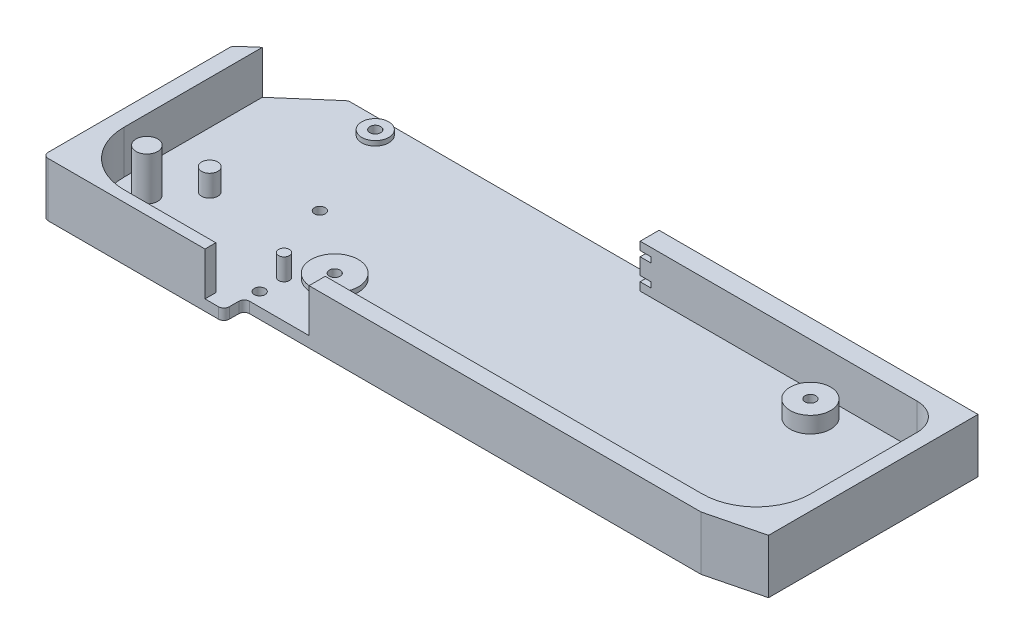
SolidWorks part; units mm, degrees
ref_plane "Front Plane" through (0, 0, 0) normal (0, 0, 1) x (1, 0, 0)
ref_plane "Top Plane" through (0, 0, 0) normal (0, 1, 0) x (1, 0, 0)
ref_plane "Right Plane" through (0, 0, 0) normal (1, 0, 0) x (0, 0, -1)
sketch "Sketch1" plane through (0, 0, 0) normal (0, 1, 0) x (1, 0, 0)
  line L0 (0, 0) -> (-23, -20)
  line L1 (-23, -20) -> (-23, -90)
  line L2 (0, 0) -> (233, 0)
  line L3 (233, 0) -> (233, -77.5)
  line L4 (44, -90) -> (-23, -90)
  line L7 (213, -82.5) -> (44, -82.5)
  line L8 (44, -82.5) -> (44, -90)
  line L10 (213, -82.5) -> (233, -77.5)
  circle A1 centre (16, -6) radius 2
  circle A2 centre (30, -40.5) radius 2
  circle A3 centre (54.5, -59.5) radius 2
  circle A4 centre (44.75, -77.5) radius 2
  circle A6 centre (187, -16) radius 2
  point P18 (187, -16)
  point P22 (44.75, -77.5)
  dimension "D1" = 4
  dimension "D4" = 4
  dimension "D7" = 4
  dimension "D10" = 4
  dimension "D15" = 4
  dimension "D23" = 20
  dimension "D2" = 16
  dimension "D3" = 6
  dimension "D5" = 34.5
  dimension "D6" = 14
  dimension "D8" = 24.5
  dimension "D9" = 19
  dimension "D11" = 18
  dimension "D12" = 14.75
  dimension "D16" = 43.5
  dimension "D17" = 132.5
  dimension "D18" = 256
  dimension "D19" = 67
  dimension "D20" = 20
  dimension "D21" = 90
  dimension "D22" = 23
  dimension "D24" = 5
  dimension "D25" = 7.5
extrude "Primary" add sketch "Sketch1" along normal blind 4
sketch "Sketch3" plane through (0, 4, 0) normal (0, 1, 0) x (1, 0, 0)
  circle A2 centre (3.5, -54.75) radius 3
  circle A3 centre (44.75, -68.5) radius 2
  circle A4 centre (44.75, -77.5) radius 2 construction
  point P11 (44.75, -77.5)
  dimension "D1" = 54.75
  dimension "D3" = 6
  dimension "D4" = 4
  dimension "D5" = 9
  dimension "D6" = 3.5
extrude "Stop Ext" add sketch "Sketch3" along normal blind 8
sketch "Sketch4" plane through (0, 4, 0) normal (0, 1, 0) x (1, 0, 0)
  line L1 (233, 0) -> (115, 0)
  line L3 (217.5, -7) -> (115, -7)
  line L4 (115, 0) -> (115, -7)
  line L11 (227.5, -56.5) -> (227.5, -17)
  line L17 (233, 0) -> (233, -77.5)
  line L18 (213, -82.5) -> (68, -82.5)
  line L19 (213, -82.5) -> (44, -82.5) construction
  line L20 (68, -82.5) -> (68, -76.5)
  line L21 (68, -76.5) -> (207.5, -76.5)
  line L22 (213, -82.5) -> (233, -77.5)
  arc A2 (207.5, -76.5) -> (227.5, -56.5) centre (207.5, -56.5) ccw
  arc A3 (227.5, -17) -> (217.5, -7) centre (217.5, -17) ccw
  point P2 (187, -16)
  point P13 (227.5, -8)
  point P15 (227.5, -7)
  point P23 (227.5, -76.5)
  dimension "D3" = 5.5
  dimension "D8" = 20
  dimension "D4" = 10
  dimension "D1" = 6
  dimension "D2" = 7
  dimension "D5" = 165
  dimension "D6" = 8
  dimension "D7" = 115
extrude "Front Ext" add sketch "Sketch4" along normal blind 16
sketch "Sketch5" plane through (0, 0, 0) normal (0, 0, -1) x (-1, 0, 0)
  line L0 (-115, 4) -> (-115, 20) construction
  line L2 (-115, 7) -> (-119, 7)
  line L3 (-115, 7) -> (-115, 9)
  line L4 (-115, 9) -> (-119, 9)
  line L5 (-119, 7) -> (-119, 9)
  line L6 (-115, 15) -> (-119, 15)
  line L7 (-115, 15) -> (-115, 17)
  line L8 (-115, 17) -> (-119, 17)
  line L9 (-119, 15) -> (-119, 17)
  line M12 (-115, 4) -> (-115, 20)
  dimension "D1" = 2
  dimension "D2" = 2
  dimension "D3" = 6
  dimension "D4" = 3
  dimension "D5" = 4
extrude "Cut-Extrude1" cut sketch "Sketch5" along normal through all from surface at -7 contours L9 L6 L8 M12
sketch "Sketch6" plane through (0, 0, 0) normal (0, 0, -1) x (-1, 0, 0)
  line L0 (-115, 15) -> (-119, 15) construction
  line L1 (-119, 9) -> (-117, 9)
  line L2 (-119, 9) -> (-119, 15)
  line L3 (-119, 15) -> (-117, 15)
  line L4 (-117, 9) -> (-117, 15)
  dimension "D1" = 2
extrude "Cut-Extrude2" cut sketch "Sketch6" against normal blind 3
sketch "Sketch7" plane through (0, 4, 0) normal (0, 1, 0) x (1, 0, 0)
  circle A1 centre (187, -16) radius 2
  circle A2 centre (187, -16) radius 7.5
  point P1 (187, -16)
  dimension "D1" = 4
  dimension "D2" = 15
extrude "Swingybit_Pin Ext" add sketch "Sketch7" along normal blind 6
sketch "Sketch8" plane through (0, 4, 0) normal (0, 1, 0) x (1, 0, 0)
  circle A0 centre (16, -6) radius 2
  circle A1 centre (16, -6) radius 5
  circle A2 centre (54.5, -59.5) radius 8.75
  circle A4 centre (54.5, -59.5) radius 2
  circle A5 centre (54.5, -59.5) radius 2 construction
  point P0 (16, -6)
  point P5 (30, -40.5)
  point P6 (54.5, -59.5)
  point P8 (-79.4755, -32.6714)
  dimension "D1" = 4
  dimension "D2" = 10
  dimension "D3" = 17.5
extrude "Wheel_Pin Ext" add sketch "Sketch8" along normal blind 1.75 contours A1 | A0 | A2 | A4
sketch "Sketch9" plane through (0, 4, 0) normal (0, 1, 0) x (1, 0, 0)
  line L0 (-23, -20) -> (-23, -86)
  line L1 (-23, -90) -> (37, -90)
  line L2 (-23, -90) -> (-23, -86)
  line L3 (3, -86) -> (37, -86)
  line L4 (37, -90) -> (37, -86)
  line L5 (-17, -66) -> (-17, -14.7826)
  line L6 (0, 0) -> (-23, -20) construction
  line L7 (-17, -14.7826) -> (-23, -20)
  arc A0 (3, -86) -> (-17, -66) centre (3, -66) cw
  point P12 (-17, -86)
  point P14 (-17, -86)
  dimension "D4" = 20
  dimension "D1" = 4
  dimension "D2" = 60
  dimension "D3" = 6
extrude "Bottom Ext" add sketch "Sketch9" along normal blind 16
fillet "Fillet1" radius 2 5 edges at (44, 2, 90) (44, 2, 82.5) (0, 2, 0) (-23, 10, 20) (-23, 10, 90)
sketch "Sketch10" plane through (0, 4, 0) normal (0, 1, 0) x (1, 0, 0)
  circle A0 centre (-7, -67.5) radius 4
  circle A1 centre (44.75, -77.5) radius 2 construction
  dimension "D3" = 8
  dimension "D1" = 10
  dimension "D2" = 7
extrude "Post Ext" add sketch "Sketch10" along normal blind 16
